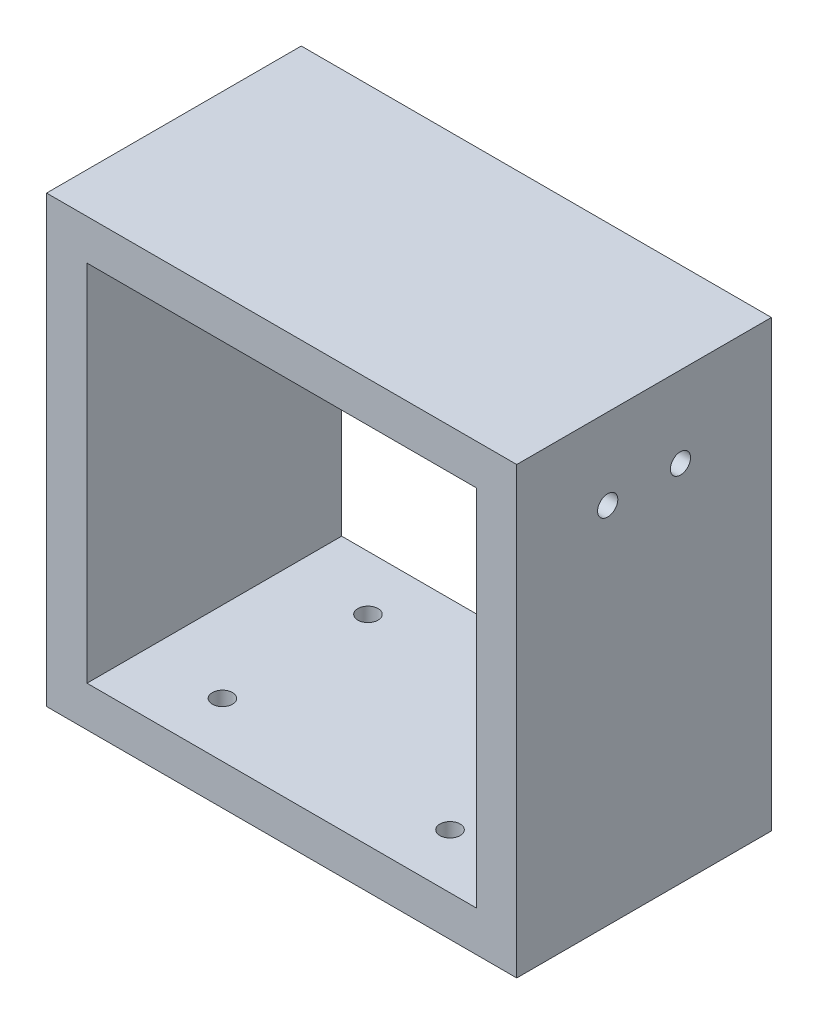
SolidWorks part; units mm, degrees
ref_plane "前视基准面" through (0, 0, 0) normal (0, 0, 1) x (1, 0, 0)
ref_plane "上视基准面" through (0, 0, 0) normal (0, 1, 0) x (1, 0, 0)
ref_plane "右视基准面" through (0, 0, 0) normal (1, 0, 0) x (0, 0, -1)
sketch "草图1" plane through (0, 0, 0) normal (0, 1, 0) x (1, 0, 0)
  line L1 (0, 0) -> (58.15, 0)
  line L2 (0, 0) -> (0, 31.5)
  line L3 (0, 31.5) -> (58.15, 31.5)
  line L4 (58.15, 0) -> (58.15, 31.5)
  dimension "D1" = 58.15
  dimension "D2" = 31.5
extrude "凸台-拉伸1" add sketch "草图1" against normal blind 55
sketch "草图2" plane through (0, 0, 0) normal (0, 0, 1) x (1, 0, 0)
  line L0 (0, -27.5) -> (53.15, -27.5) construction
  line L1 (0, -55) -> (0, 0) construction
  line L2 (29.075, 0) -> (29.075, -40.7336) construction
  line L3 (0, 0) -> (58.15, 0) construction
  line L4 (58.15, -55) -> (58.15, 0) construction
  line L5 (5, -50) -> (53.15, -50)
  line L6 (5, -50) -> (5, -5)
  line L7 (5, -5) -> (53.15, -5)
  line L8 (53.15, -50) -> (53.15, -5)
  line L9 (29.075, -5) -> (29.075, -50) construction
  line L10 (5, -27.5) -> (53.15, -27.5) construction
  point P8 (29.075, -27.5)
  dimension "D1" = 5
  dimension "D2" = 5
  dimension "D3" = 5
extrude "切除-拉伸1" cut sketch "草图2" against normal up to surface (31.5 mm away) up to face at (29.075, -27.5, -31.5)
sketch "草图4" plane through (0, -55, 0) normal (0, -1, 0) x (1, 0, 0)
  circle A0 centre (15, -6.75) radius 1.25
  circle A1 centre (15, -24.75) radius 1.25
  circle A2 centre (43.15, -6.75) radius 1.25
  circle A3 centre (43.15, -24.75) radius 1.25
extrude "切除-拉伸2" cut sketch "草图4" against normal blind 10
sketch "草图5" plane through (53.15, 0, 0) normal (-1, 0, 0) x (0, 0, 1)
  circle A0 centre (-20.25, -10) radius 1.25
  circle A1 centre (-11.25, -10) radius 1.25
  point P4 (0, 0)
  point P5 (0, 0)
  dimension "D1" = 2.5
  dimension "D2" = 2.5
extrude "切除-拉伸3" cut sketch "草图5" against normal blind 10
sketch "草图6" plane through (5, 0, 0) normal (1, 0, 0) x (0, 0, -1)
  circle A0 centre (11.25, -10) radius 1.25
  circle A1 centre (20.25, -10) radius 1.25
  point P4 (0, 0)
  point P5 (0, 0)
  dimension "D1" = 2.5
  dimension "D2" = 2.5
extrude "切除-拉伸4" cut sketch "草图6" against normal blind 10
